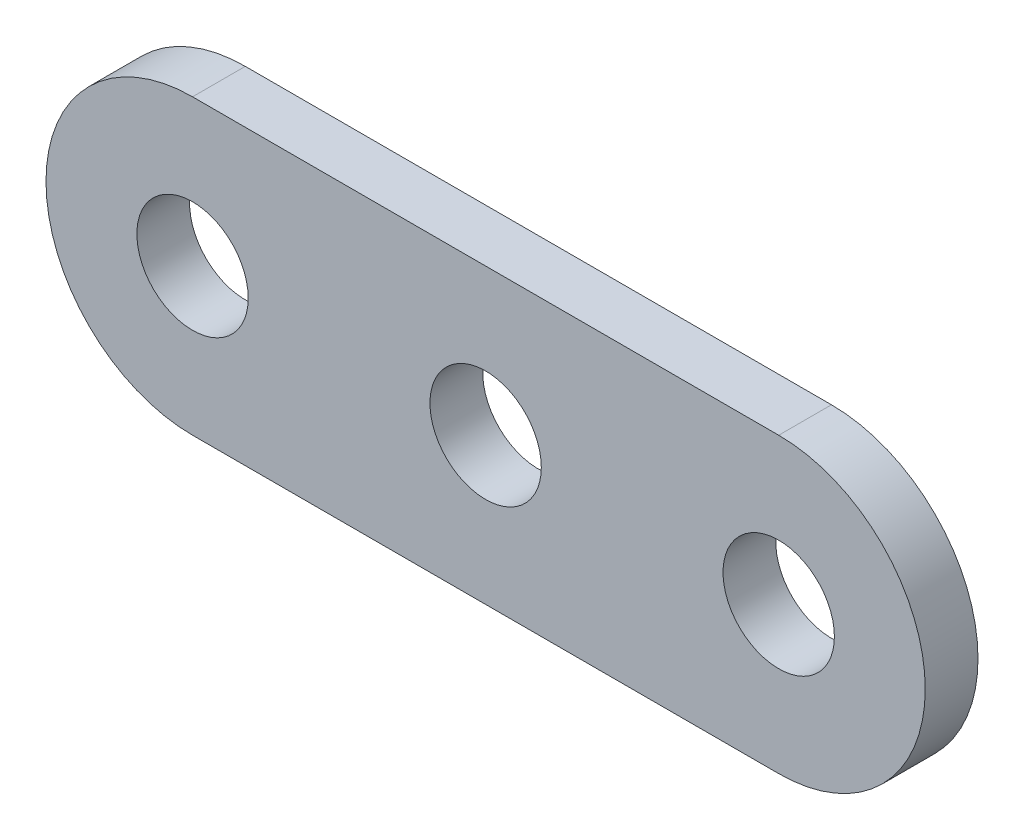
SolidWorks part; units mm, degrees
ref_plane "Front Plane" through (0, 0, 0) normal (0, 0, 1) x (1, 0, 0)
ref_plane "Top Plane" through (0, 0, 0) normal (0, 1, 0) x (1, 0, 0)
ref_plane "Right Plane" through (0, 0, 0) normal (1, 0, 0) x (0, 0, -1)
sketch "Sketch1" plane through (0, 0, 0) normal (0, 0, 1) x (1, 0, 0)
  line L0 (0, 0) -> (50000, 0) construction
  line L1 (0, 0) -> (0, -50000) construction
  line L2 (-12.7, 6.35) -> (12.7, 6.35)
  line L3 (-12.7, -6.35) -> (12.7, -6.35)
  arc A0 (12.7, -6.35) -> (12.7, 6.35) centre (12.7, 0) ccw
  arc A1 (-12.7, -6.35) -> (-12.7, 6.35) centre (-12.7, 0) cw
  circle A2 centre (0, 0) radius 2.413
  circle A3 centre (12.7, 0) radius 2.413
  circle A4 centre (-12.7, 0) radius 2.413
  dimension "D2" = 6.35
  dimension "D3" = 4.826
  dimension "D1" = 25.4
extrude "Boss-Extrude1" add sketch "Sketch1" along normal blind 2.286
